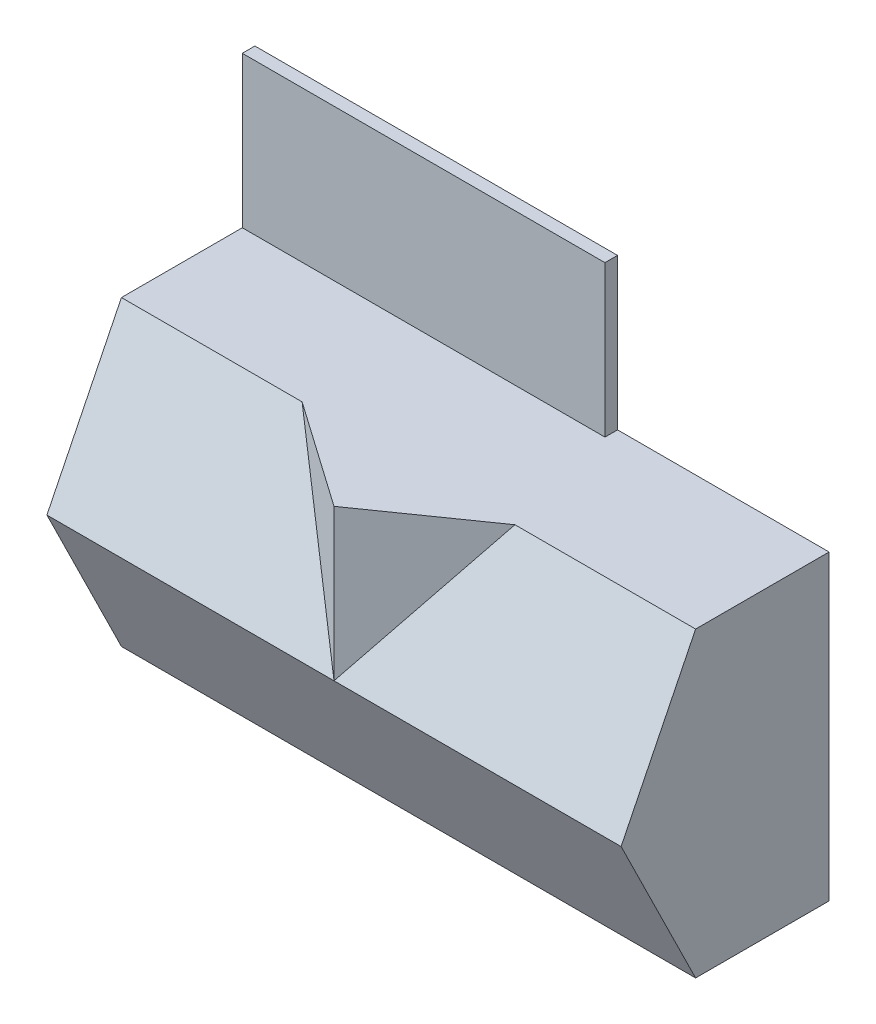
SolidWorks part; units mm, degrees
ref_plane "Front Plane" through (0, 0, 0) normal (0, 0, 1) x (1, 0, 0)
ref_plane "Top Plane" through (0, 0, 0) normal (0, 1, 0) x (1, 0, 0)
ref_plane "Right Plane" through (0, 0, 0) normal (1, 0, 0) x (0, 0, -1)
sketch "Sketch3" plane through (0, 0, 0) normal (0, 0, 1) x (1, 0, 0)
  line L0 (152.4, 152.4) -> (4550.005, 152.4)
  line L1 (0, 0) -> (11582.4, 0)
  line L2 (0, 0) -> (0, 6096)
  line L3 (0, 6096) -> (11582.4, 6096)
  line L4 (11582.4, 0) -> (11582.4, 6096)
  line L5 (4550.005, 152.4) -> (4550.005, 2596.7986)
  line L6 (4550.005, 2596.7986) -> (5842, 2596.7986)
  line L7 (11582.4, 6096) -> (7620, 6096) construction
  line L8 (7620, 6096) -> (5842, 6096) construction
  line L9 (5842, 5943.6) -> (5842, 3511.1986)
  line L10 (5943.6, 3511.1986) -> (10284.7543, 3511.1986)
  line L11 (7620, 5943.6) -> (7620, 3612.7986)
  line L12 (4550.005, 2596.7986) -> (5842, 2596.7986) construction
  line L13 (7315.2, 2495.1986) -> (7315.2, 152.4)
  line L14 (5842, 3511.1986) -> (5842, 2596.7986)
  line L15 (10386.3543, 3511.1986) -> (10386.3543, 2596.7986)
  line L16 (9786.5812, 3511.1986) -> (9786.5812, 2596.7986) construction
  line L17 (0, 6096) -> (0, 9448.8) construction
  line L18 (0, 9448.8) -> (6388.492, 9448.8) construction
  line L19 (6388.492, 9448.8) -> (6388.492, 6096) construction
  line L20 (11430, 152.4) -> (11430, 2495.1986)
  line L21 (3310.1163, 2590.8) -> (0, 2590.8) construction
  line L22 (152.4, 5943.6) -> (5842, 5943.6)
  line L23 (152.4, 152.4) -> (152.4, 5943.6)
  line L24 (4651.605, 152.4) -> (4651.605, 2495.1986)
  line L25 (4651.605, 2495.1986) -> (7315.2, 2495.1986)
  line L26 (7416.8, 2495.1986) -> (7416.8, 152.4)
  line L27 (10284.7543, 3511.1986) -> (10284.7543, 2596.7986)
  line L28 (5943.6, 3612.7986) -> (7620, 3612.7986)
  line L29 (5943.6, 5943.6) -> (5943.6, 3612.7986)
  line L30 (7721.6, 5943.6) -> (7721.6, 3612.7986)
  line L31 (7620, 6096) -> (7620, 3505.2) construction
  line L32 (7721.6, 6096) -> (7721.6, 3505.2) construction
  line L33 (5842, 6096) -> (5842, 3511.1986) construction
  line L34 (5943.6, 6096) -> (5943.6, 3511.1986) construction
  line L35 (5943.6, 5943.6) -> (7620, 5943.6)
  line L36 (152.4, 5943.6) -> (11430, 5943.6) construction
  line L37 (7721.6, 5943.6) -> (11430, 5943.6)
  line L38 (5842, 3612.7986) -> (11582.4, 3612.7986) construction
  line L39 (7721.6, 3612.7986) -> (11430, 3612.7986)
  line L40 (11430, 3612.7986) -> (11430, 5943.6)
  line L41 (11430, 152.4) -> (11430, 5943.6) construction
  line L42 (5842, 3511.1986) -> (11582.4, 3511.1986) construction
  line L43 (10386.3543, 3511.1986) -> (11430, 3511.1986)
  line L44 (10386.3543, 2596.7986) -> (11430, 2596.7986)
  line L45 (4550.005, 2596.7986) -> (11582.4, 2596.7986) construction
  line L46 (11430, 2596.7986) -> (11430, 3511.1986)
  line L47 (4651.605, 2495.1986) -> (11582.4, 2495.1986) construction
  line L48 (7315.2, 2596.7986) -> (7315.2, 0) construction
  line L49 (7416.8, 2596.7986) -> (7416.8, 0) construction
  line L50 (7416.8, 2495.1986) -> (11430, 2495.1986)
  line L51 (7416.8, 152.4) -> (11430, 152.4)
  line L52 (152.4, 152.4) -> (11430, 152.4) construction
  line L53 (4550.005, 0) -> (4550.005, 2596.7986) construction
  line L54 (4651.605, 0) -> (4651.605, 2495.1986) construction
  line L55 (4651.605, 152.4) -> (7315.2, 152.4)
  line L56 (5943.6, 3511.1986) -> (5943.6, 2596.7986)
  line L57 (5943.6, 2596.7986) -> (10284.7543, 2596.7986)
  line L58 (5943.6, 2596.7986) -> (7315.2, 2596.7986) construction
  dimension "D1" = 11582.4
  dimension "D2" = 6096
  dimension "D4" = 3962.4
  dimension "D5" = 1778
  dimension "D7" = 914.4
  dimension "D8" = 152.4
  dimension "D9" = 101.6
  dimension "D10" = 101.6
  dimension "D11" = 101.6
  dimension "D12" = 101.6
  dimension "D13" = 101.6
extrude "Boss-Extrude1" add sketch "Sketch3" along normal blind 2438.4 contours L1 L4 L3 L2 L55 L24 L25 L13 L51 L26 L50 L20 L46 L44 L15 L43 L40 L39 L30 L37 L10 L27 L6 L5 L0 L23 L22 L9 L29 L35 L11 L28
sketch "Sketch4" plane through (0, 0, 0) normal (0, 0, -1) x (-1, 0, 0)
  line L1 (-11582.4, 6096) -> (0, 6096)
  line L2 (-11582.4, 6096) -> (-11582.4, 0)
  line L3 (-11582.4, 0) -> (0, 0)
  line L4 (0, 6096) -> (0, 0)
extrude "Boss-Extrude2" add sketch "Sketch4" along normal blind 254
sketch "Sketch5" plane through (0, 0, 0) normal (0, 0, 1) x (1, 0, 0)
  line L1 (3330.805, 2596.7986) -> (152.4, 2596.7986)
  line L2 (152.4, 152.4) -> (152.4, 5943.6) construction
  line L3 (152.4, 2596.7986) -> (152.4, 2495.1986)
  line L4 (152.4, 152.4) -> (152.4, 5943.6) construction
  line L5 (152.4, 2495.1986) -> (3330.805, 2495.1986)
  line L6 (3330.805, 2495.1986) -> (3330.805, 2596.7986)
extrude "Boss-Extrude3" add sketch "Sketch5" along normal blind 1016
sketch "Sketch6" plane through (0, 0, 0) normal (-1, 0, 0) x (0, 0, 1)
  line L0 (2438.4, 6096) -> (2438.4, 0)
  line L1 (2438.4, 6096) -> (3941.5073, 3048)
  line L2 (2438.4, 3048) -> (3941.5073, 3048) construction
  line L3 (3941.5073, 3048) -> (2438.4, 0)
  dimension "D1" = 26.25
extrude "Boss-Extrude4" add sketch "Sketch6" against normal up to surface (11582.4 mm away) up to face at (11582.4, 3048, 1092.2)
sketch "Sketch7" plane through (0, 6096, 0) normal (0, 1, 0) x (1, 0, 0)
  line L0 (0, 254) -> (7315.2, 254) construction
  line L1 (0, 254) -> (11582.4, 254) construction
  line L2 (7315.2, 254) -> (7315.2, -2438.4) construction
  line L3 (0, -2438.4) -> (11582.4, -2438.4) construction
  line L4 (7937.8596, -2438.4) -> (5791.2, -3941.5073)
  line L5 (11582.4, -3941.5073) -> (0, -3941.5073) construction
  line L6 (5791.2, -3941.5073) -> (5791.2, -2438.4) construction
  line L7 (3644.5404, -2438.4) -> (5791.2, -3941.5073)
  line L8 (7937.8596, -2438.4) -> (3644.5404, -2438.4)
  dimension "D1" = 55
extrude "Boss-Extrude5" add sketch "Sketch7" against normal up to surface (3048 mm away)
sketch "Sketch8" plane through (0, 0, -254) normal (0, 0, -1) x (-1, 0, 0)
  line L1 (0, 6096) -> (-7315.2, 6096)
  line L2 (0, 6096) -> (0, 9144)
  line L3 (0, 9144) -> (-7315.2, 9144)
  line L4 (-7315.2, 6096) -> (-7315.2, 9144)
  dimension "D1" = 7315.2
  dimension "D2" = 3048
extrude "Boss-Extrude6" add sketch "Sketch8" against normal blind 254 separate body
